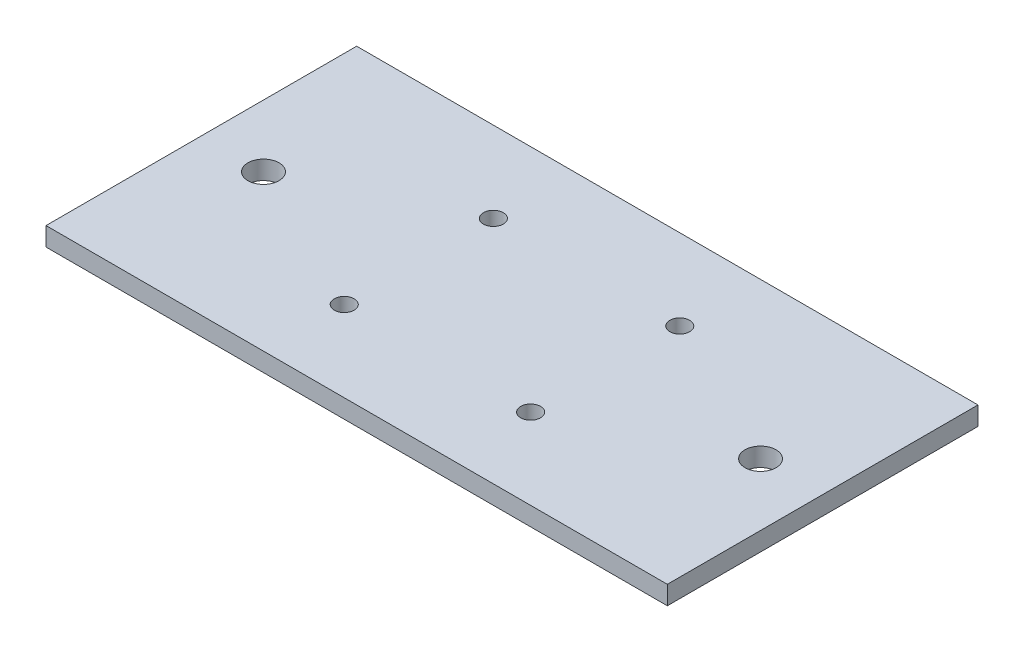
SolidWorks part; units mm, degrees
ref_plane "Front Plane" through (0, 0, 0) normal (0, 0, 1) x (1, 0, 0)
ref_plane "Top Plane" through (0, 0, 0) normal (0, 1, 0) x (1, 0, 0)
ref_plane "Right Plane" through (0, 0, 0) normal (1, 0, 0) x (0, 0, -1)
sketch "Sketch2" plane through (0, 0, 0) normal (0, 1, 0) x (1, 0, 0)
  line L1 (-50, 25) -> (50, 25)
  line L2 (-50, 25) -> (-50, -25)
  line L3 (-50, -25) -> (50, -25)
  line L4 (50, 25) -> (50, -25)
  line L5 (-50, 25) -> (50, -25) construction
  line L6 (-50, -25) -> (50, 25) construction
  point P0 (0, 0)
extrude "Boss-Extrude2" add sketch "Sketch2" along normal blind 3
sketch "Sketch5" plane through (0, 3, 0) normal (0, 1, 0) x (1, 0, 0)
  line L0 (-40, 0) -> (40, 0) construction
  line L1 (-15, 12) -> (15, 12) construction
  line L2 (15, 12) -> (15, -12) construction
  line L3 (-15, -12) -> (15, -12) construction
  circle A0 centre (-40, 0) radius 2.5
  circle A1 centre (40, 0) radius 2.5
  circle A2 centre (-15, 12) radius 1.6
  circle A3 centre (-15, -12) radius 1.6
  circle A4 centre (15, 12) radius 1.6
  circle A5 centre (15, -12) radius 1.6
extrude "Cut-Extrude1" cut sketch "Sketch5" against normal blind 3
